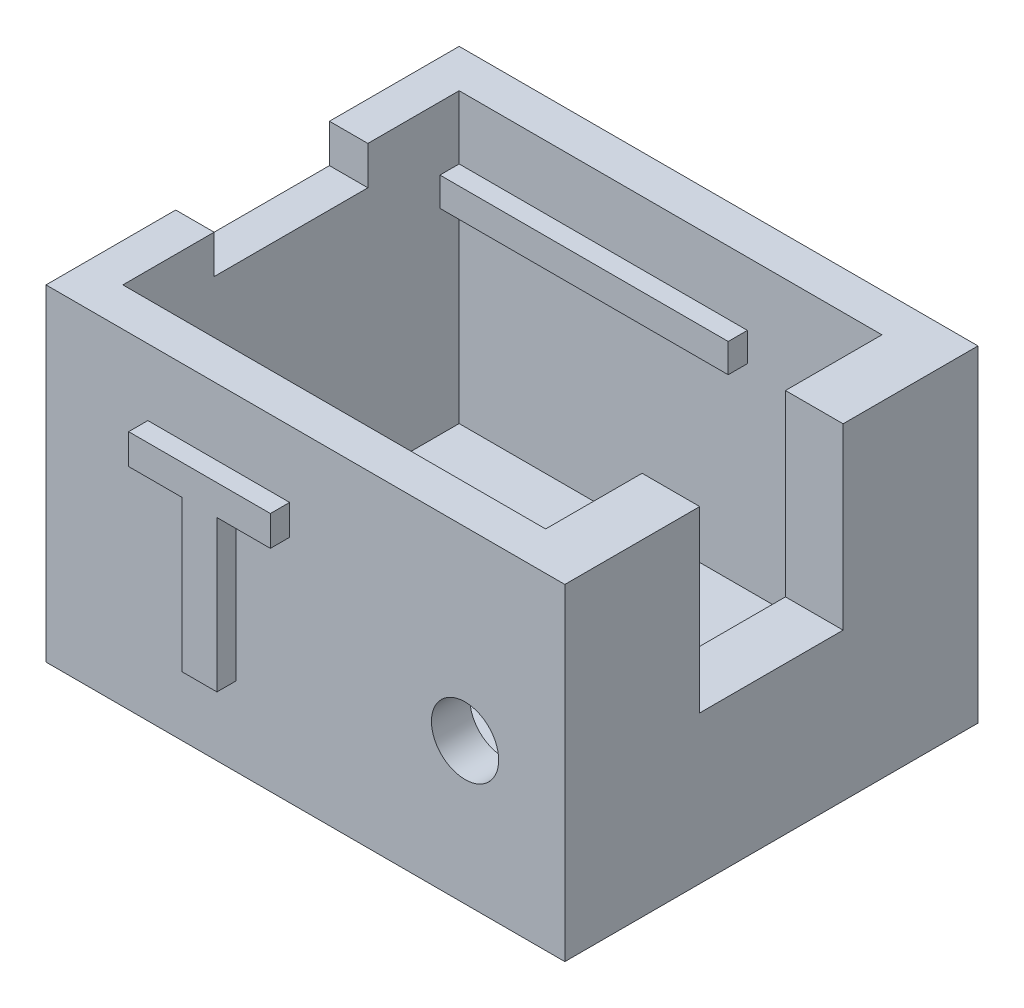
SolidWorks part; units mm, degrees
ref_plane "Спереди" through (0, 0, 0) normal (0, 0, 1) x (1, 0, 0)
ref_plane "Сверху" through (0, 0, 0) normal (0, 1, 0) x (1, 0, 0)
ref_plane "Справа" through (0, 0, 0) normal (1, 0, 0) x (0, 0, -1)
sketch "Sketch1" plane through (0, 0, 0) normal (0, 1, 0) x (1, 0, 0)
  line L1 (-5.804, 7.255) -> (21.196, 7.255)
  line L2 (-5.804, 7.255) -> (-5.804, -14.245)
  line L3 (-5.804, -14.245) -> (21.196, -14.245)
  line L4 (21.196, 7.255) -> (21.196, -14.245)
  dimension "D1" = 21.5
  dimension "D2" = 27
extrude "Boss-Extrude1" add sketch "Sketch1" along normal blind 2
sketch "Sketch2" plane through (0, 2, 0) normal (0, 1, 0) x (1, 0, 0)
  line L1 (-5.804, 7.255) -> (21.196, 7.255)
  line L2 (-5.804, 7.255) -> (-5.804, -14.245)
  line L3 (-5.804, -14.245) -> (21.196, -14.245)
  line L4 (21.196, 7.255) -> (21.196, -14.245)
  line L5 (-3.804, 5.255) -> (18.196, 5.255)
  line L6 (-3.804, 5.255) -> (-3.804, -12.245)
  line L7 (-3.804, -12.245) -> (18.196, -12.245)
  line L8 (18.196, 5.255) -> (18.196, -12.245)
  dimension "D1" = 2
  dimension "D2" = 2
  dimension "D3" = 2
  dimension "D4" = 3
extrude "Boss-Extrude2" add sketch "Sketch2" along normal blind 15
sketch "Sketch3" plane through (0, 0, -5.255) normal (0, 0, 1) x (1, 0, 0)
  line L0 (-3.804, 17) -> (-3.804, 2) construction
  line L1 (-3.804, 13.7) -> (11.196, 13.7)
  line L2 (-3.804, 13.7) -> (-3.804, 12.2)
  line L3 (-3.804, 12.2) -> (11.196, 12.2)
  line L4 (11.196, 13.7) -> (11.196, 12.2)
  line L6 (18.196, 17) -> (-3.804, 17) construction
  dimension "D1" = 3.3
  dimension "D2" = 1.5
  dimension "D3" = 15
extrude "Boss-Extrude3" add sketch "Sketch3" along normal blind 1
sketch "Sketch4" plane through (0, 0, 12.245) normal (0, 0, -1) x (-1, 0, 0)
  line L1 (-11.196, 12.7) -> (3.804, 12.7)
  line L2 (-11.196, 12.7) -> (-11.196, 13.7)
  line L3 (-11.196, 13.7) -> (3.804, 13.7)
  line L4 (3.804, 12.7) -> (3.804, 13.7)
  line L5 (3.804, 17) -> (3.804, 2) construction
  line L6 (3.804, 17) -> (-18.196, 17) construction
  dimension "D1" = 1
  dimension "D2" = 3.3
  dimension "D3" = 15
extrude "Boss-Extrude4" add sketch "Sketch4" along normal blind 1
sketch "Sketch7" plane through (0, 0, 14.245) normal (0, 0, 1) x (1, 0, 0)
  circle A0 centre (16.0029, 7.3619) radius 1.75
  dimension "D1" = 3.5
extrude "Cut-Extrude2" cut sketch "Sketch7" against normal blind 2
sketch "Sketch8" plane through (0, 17, 0) normal (0, 1, 0) x (1, 0, 0)
  line L0 (18.196, -12.245) -> (18.196, 5.255) construction
  line L1 (18.196, 0.235) -> (21.196, 0.235)
  line L2 (18.196, 0.235) -> (18.196, -7.225)
  line L3 (18.196, -7.225) -> (21.196, -7.225)
  line L4 (21.196, 0.235) -> (21.196, -7.225)
  line L5 (21.196, -14.245) -> (21.196, 7.255) construction
  line L6 (21.196, 0.235) -> (21.196, 7.255) construction
  line L7 (21.196, -7.225) -> (21.196, -14.245) construction
  dimension "D1" = 7.46
extrude "Cut-Extrude3" cut sketch "Sketch8" against normal blind 9.3
sketch "Sketch9" plane through (-5.804, 0, 0) normal (-1, 0, 0) x (0, 0, 1)
  text T0 "<b>NU</b>" font "Arial" height in points 36
extrude "Boss-Extrude5" add sketch "Sketch9" along normal blind 1
sketch "Sketch10" plane through (0, 0, 14.245) normal (0, 0, 1) x (1, 0, 0)
  text T0 "<b>T</b>" font "Arial" height in points 36
extrude "Boss-Extrude6" add sketch "Sketch10" along normal blind 1
sketch "Sketch11" plane through (0, 17, 0) normal (0, 1, 0) x (1, 0, 0)
  line L0 (-3.804, 5.255) -> (-3.804, -12.245) construction
  line L1 (-3.804, -7.495) -> (-5.804, -7.495)
  line L2 (-3.804, -7.495) -> (-3.804, 0.505)
  line L3 (-3.804, 0.505) -> (-5.804, 0.505)
  line L4 (-5.804, -7.495) -> (-5.804, 0.505)
  line L5 (-5.804, 7.255) -> (-5.804, -14.245) construction
  line L6 (-5.3814, -7.495) -> (-5.3814, -14.245) construction
  line L7 (-5.804, -14.245) -> (21.196, -14.245) construction
  line L8 (-5.3814, 0.505) -> (-5.3814, 7.255) construction
  line L9 (21.196, 7.255) -> (-5.804, 7.255) construction
  dimension "D1" = 8
extrude "Cut-Extrude4" cut sketch "Sketch11" against normal blind 2
